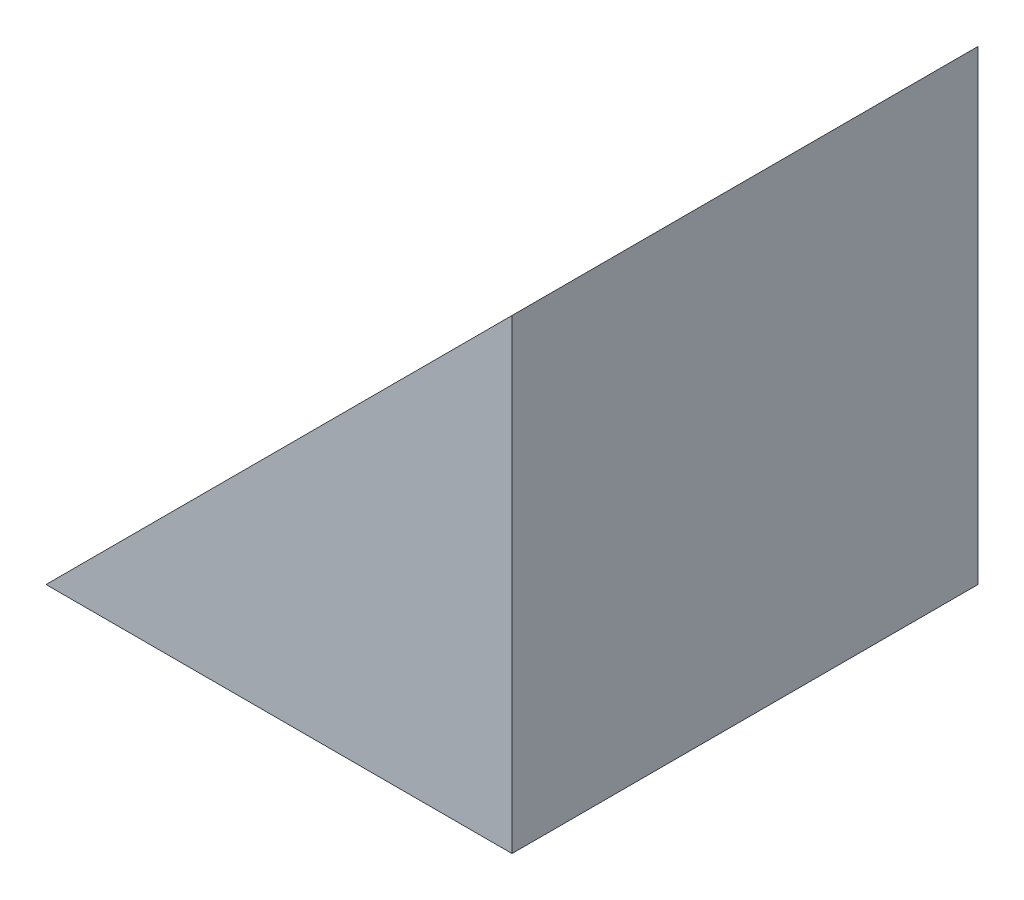
SolidWorks part; units mm, degrees
ref_plane "前视基准面" through (0, 0, 0) normal (0, 0, 1) x (1, 0, 0)
ref_plane "上视基准面" through (0, 0, 0) normal (0, 1, 0) x (1, 0, 0)
ref_plane "右视基准面" through (0, 0, 0) normal (1, 0, 0) x (0, 0, -1)
sketch "草图1" plane through (0, 0, 0) normal (0, 0, 1) x (1, 0, 0)
  line L0 (34.9428, 26.5558) -> (34.9428, 36.5558)
  line L1 (34.9428, 26.5558) -> (24.9428, 26.5558)
  line L2 (24.9428, 26.5558) -> (34.9428, 36.5558)
  dimension "D1" = 10
  dimension "D2" = 10
extrude "凸台-拉伸1" add sketch "草图1" along normal blind 10
